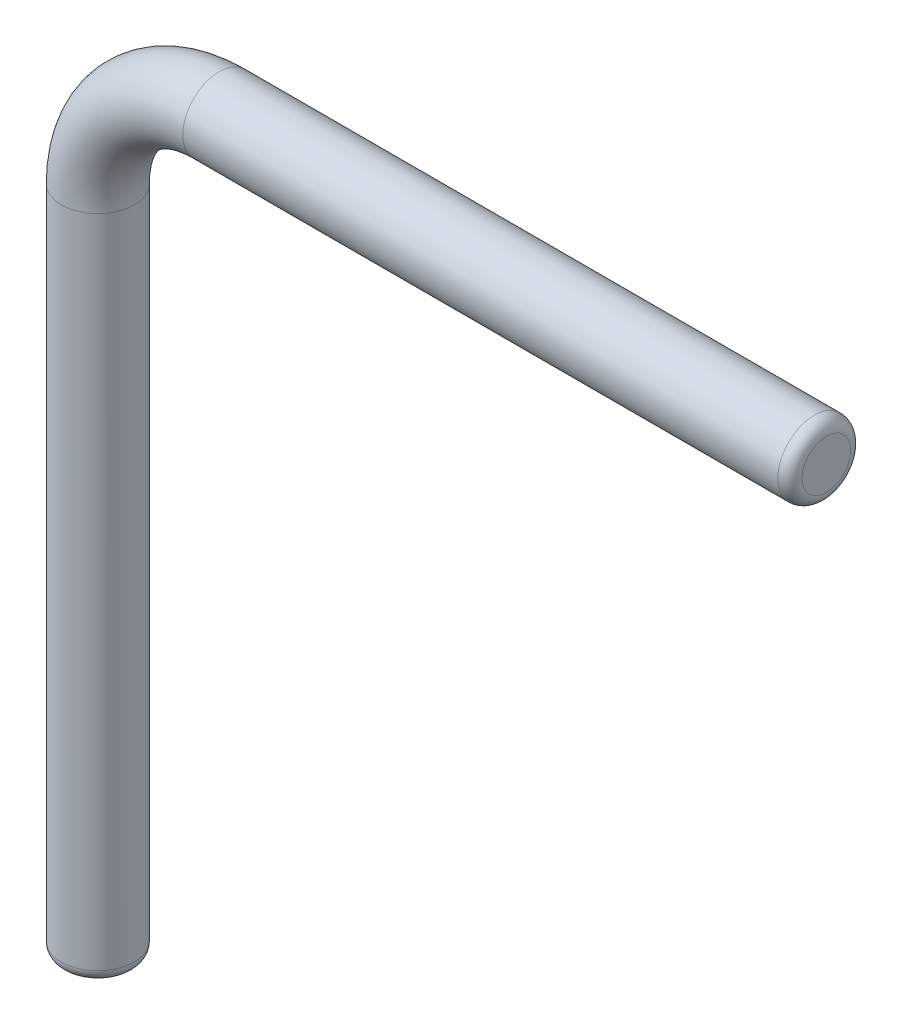
SolidWorks part; units mm, degrees
ref_plane "Ön Düzlem" through (0, 0, 0) normal (0, 0, 1) x (1, 0, 0)
ref_plane "Üst Düzlem" through (0, 0, 0) normal (0, 1, 0) x (1, 0, 0)
ref_plane "Sağ Düzlem" through (0, 0, 0) normal (1, 0, 0) x (0, 0, -1)
sketch "Sketch3" plane through (0, 0, 0) normal (0, 0, 1) x (1, 0, 0)
  line L0 (0, 0) -> (0, 5.5)
  line L1 (1, 6.5) -> (6, 6.5)
  arc A0 (0, 5.5) -> (1, 6.5) centre (1, 5.5) cw
  point P6 (0, 6.5)
  dimension "D3" = 1
  dimension "D1" = 6.5
  dimension "D2" = 6
sketch "Sketch4" plane through (0, 0, 0) normal (0, 1, 0) x (1, 0, 0)
  circle A0 centre (0, 0) radius 0.3
  dimension "D1" = 0.6
sweep "Sweep1" add profiles "Sketch4" path "Sketch3"
fillet "Fillet1" radius 0.1 2 edges at (6, 6.5, 0.3) (0, 0, 0.3)
